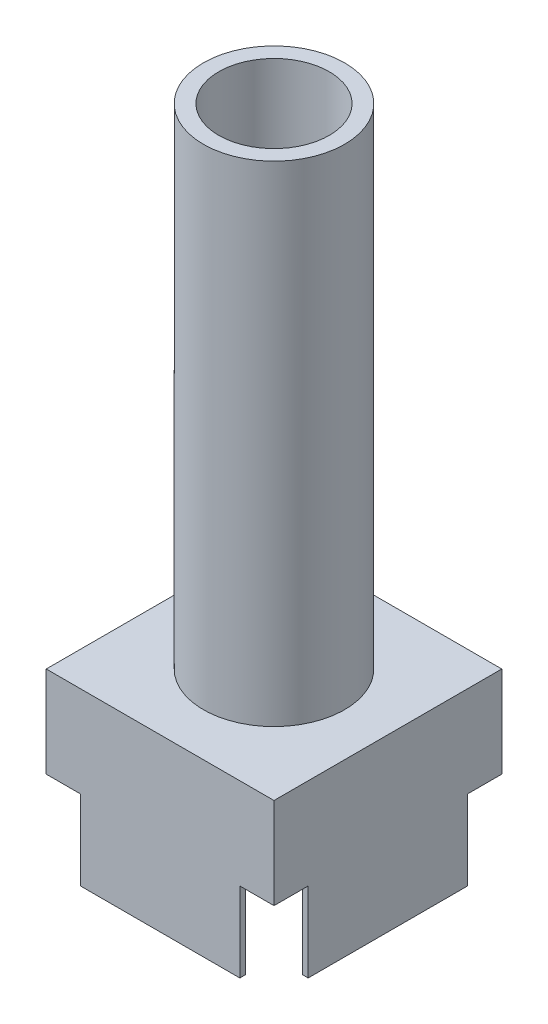
SolidWorks part; units mm, degrees
ref_plane "前基準面" through (0, 0, 0) normal (0, 0, 1) x (1, 0, 0)
ref_plane "上基準面" through (0, 0, 0) normal (0, 1, 0) x (1, 0, 0)
ref_plane "右基準面" through (0, 0, 0) normal (1, 0, 0) x (0, 0, -1)
sketch "草圖1" plane through (0, 0, 0) normal (0, 1, 0) x (1, 0, 0)
  line L1 (0, 0) -> (20, 0)
  line L2 (0, 0) -> (0, 20)
  line L3 (0, 20) -> (20, 20)
  line L4 (20, 0) -> (20, 20)
  line L5 (0.5, 0.5) -> (19.5, 0.5)
  line L6 (0.5, 0.5) -> (0.5, 19.5)
  line L7 (0.5, 19.5) -> (19.5, 19.5)
  line L8 (19.5, 0.5) -> (19.5, 19.5)
  dimension "D1" = 20
  dimension "D2" = 20
  dimension "D3" = 19
  dimension "D4" = 19
  dimension "D5" = 0.5
  dimension "D6" = 0.5
extrude "填料-伸長1" add sketch "草圖1" along normal blind 7
ref_plane "平面1" through (0, 7, 0) normal (0, 1, 0) x (1, 0, 0)
sketch "草圖3" plane through (0, 7, 0) normal (0, 1, 0) x (1, 0, 0)
  line L1 (0, 0) -> (20, 0)
  line L2 (0, 0) -> (0, 20)
  line L3 (0, 20) -> (20, 20)
  line L4 (20, 0) -> (20, 20)
extrude "填料-伸長2" add sketch "草圖3" along normal blind 8
sketch "草圖4" plane through (0, 15, 0) normal (0, 1, 0) x (1, 0, 0)
  line L0 (20, 0) -> (20, 20) construction
  line L1 (20, 20) -> (0, 20) construction
  circle A0 centre (10, 10) radius 6.2
  dimension "D1" = 12.4
  dimension "D2" = 10
  dimension "D3" = 10
extrude "填料-伸長3" add sketch "草圖4" along normal blind 43
sketch "草圖5" plane through (0, 58, 0) normal (0, 1, 0) x (1, 0, 0)
  line L0 (10, 10) -> (10, 11.7)
  line L1 (8, 11.7) -> (12, 11.7)
  circle A0 centre (10, 10) radius 4.85
  point P6 (10, 11.7)
  dimension "D3" = 9.7
  dimension "D1" = 1.7
  dimension "D2" = 4
extrude "除料-伸長1" cut sketch "草圖5" against normal blind 18
ref_plane "平面2" through (0, 7, 0) normal (0, 1, 0) x (1, 0, 0)
sketch "草圖6" plane through (0, 7, 0) normal (0, 1, 0) x (1, 0, 0)
  line L1 (0, 20) -> (3, 20)
  line L2 (0, 20) -> (0, 17)
  line L3 (0, 17) -> (3, 17)
  line L4 (3, 20) -> (3, 17)
  line L5 (20, 0) -> (17, 0)
  line L6 (20, 0) -> (20, 3)
  line L7 (20, 3) -> (17, 3)
  line L8 (17, 0) -> (17, 3)
  line L9 (20, 20) -> (17, 20)
  line L10 (20, 20) -> (20, 17)
  line L11 (20, 17) -> (17, 17)
  line L12 (17, 20) -> (17, 17)
  line L13 (0, 0) -> (3, 0)
  line L14 (0, 0) -> (0, 3)
  line L15 (0, 3) -> (3, 3)
  line L16 (3, 0) -> (3, 3)
  dimension "D1" = 3
  dimension "D2" = 3
  dimension "D3" = 3
  dimension "D4" = 3
extrude "除料-伸長2" cut sketch "草圖6" against normal blind 10
